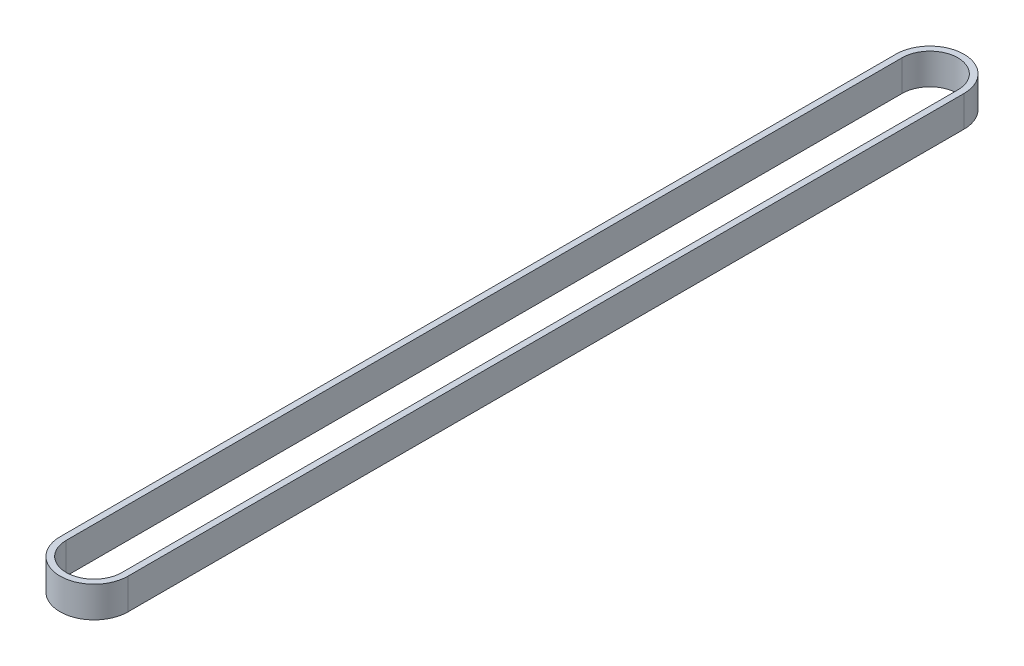
SolidWorks part; units mm, degrees
ref_plane "Front Plane" through (0, 0, 0) normal (0, 0, 1) x (1, 0, 0)
ref_plane "Top Plane" through (0, 0, 0) normal (0, 1, 0) x (1, 0, 0)
ref_plane "Right Plane" through (0, 0, 0) normal (1, 0, 0) x (0, 0, -1)
sketch "Sketch1" plane through (0, 0, 0) normal (0, 1, 0) x (1, 0, 0)
  line L0 (0, 0) -> (0, -270) construction
  line L5 (-11, -270) -> (-11, 0)
  line L6 (11, 0) -> (11, -270)
  line L7 (-9, -270) -> (-9, 0)
  line L8 (9, 0) -> (9, -270)
  arc A0 (9, 0) -> (-9, 0) centre (0, 0) ccw
  arc A1 (11, 0) -> (-11, 0) centre (0, 0) ccw
  arc A2 (-9, -270) -> (9, -270) centre (0, -270) ccw
  arc A3 (-11, -270) -> (11, -270) centre (0, -270) ccw
  dimension "D1" = 18
  dimension "D2" = 22
  dimension "D4" = 22
  dimension "D5" = 18
  dimension "D3" = 270
extrude "Boss-Extrude1" add sketch "Sketch1" along normal blind 10
